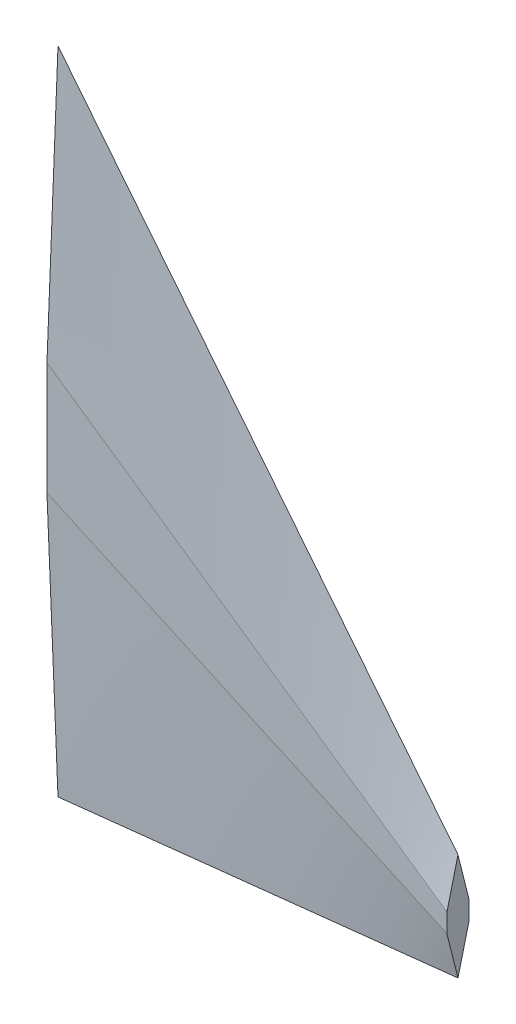
SolidWorks part; units mm, degrees
material "Hexcel AS4C (3000 Filaments)"
ref_plane "Front Plane" through (0, 0, 0) normal (0, 0, 1) x (1, 0, 0)
ref_plane "Top Plane" through (0, 0, 0) normal (0, 1, 0) x (1, 0, 0)
ref_plane "Right Plane" through (0, 0, 0) normal (1, 0, 0) x (0, 0, -1)
sketch "Sketch1" plane through (0, 0, 0) normal (1, 0, 0) x (0, 0, -1)
  line L0 (0, 74.29) -> (2.5212, 12.87)
  line L1 (2.5212, 12.87) -> (2.5212, -12.87)
  line L2 (2.5212, -12.87) -> (0, -74.29)
  line L3 (0, 10.685) -> (0, 13.7664) construction
  line L4 (0, 74.29) -> (0, -74.29) construction
  line L5 (-2.5212, -12.87) -> (0, -74.29)
  line L6 (-2.5212, 12.87) -> (-2.5212, -12.87)
  line L7 (0, 74.29) -> (-2.5212, 12.87)
  point P4 (2.5212, 0)
  point P7 (0, 0)
  dimension "D1" = 25.74
  dimension "D2" = 148.58
ref_plane "Plane1" through (91.39, 0, 0) normal (1, 0, 0) x (0, 0, -1)
sketch "Sketch2" plane through (91.39, 0, 0) normal (1, 0, 0) x (0, 0, -1)
  line L2 (0, -40.04) -> (0, -64.424) construction
  line L8 (0, -64.424) -> (2.5212, -54.391)
  line L9 (0, -199989.315) -> (0, 200013.7664) construction
  line L10 (2.5212, 12.87) -> (2.5212, -12.87) construction
  line L11 (2.5212, -54.391) -> (2.5212, -50.073)
  line L12 (2.5212, -50.073) -> (0, -40.04)
  line L13 (-2.5212, -50.073) -> (0, -40.04)
  line L14 (-2.5212, -54.391) -> (-2.5212, -50.073)
  line L15 (0, -64.424) -> (-2.5212, -54.391)
  point P8 (0, -52.232)
  point P9 (2.5212, -52.232)
  dimension "D1" = 24.384
  dimension "D2" = 4.318
  dimension "D3" = 114.33
loft "Loft1" add profiles "Sketch1", "Sketch2"
ref_plane "Plane2" through (0, -74.422, 0) normal (0, 1, 0) x (1, 0, 0)
